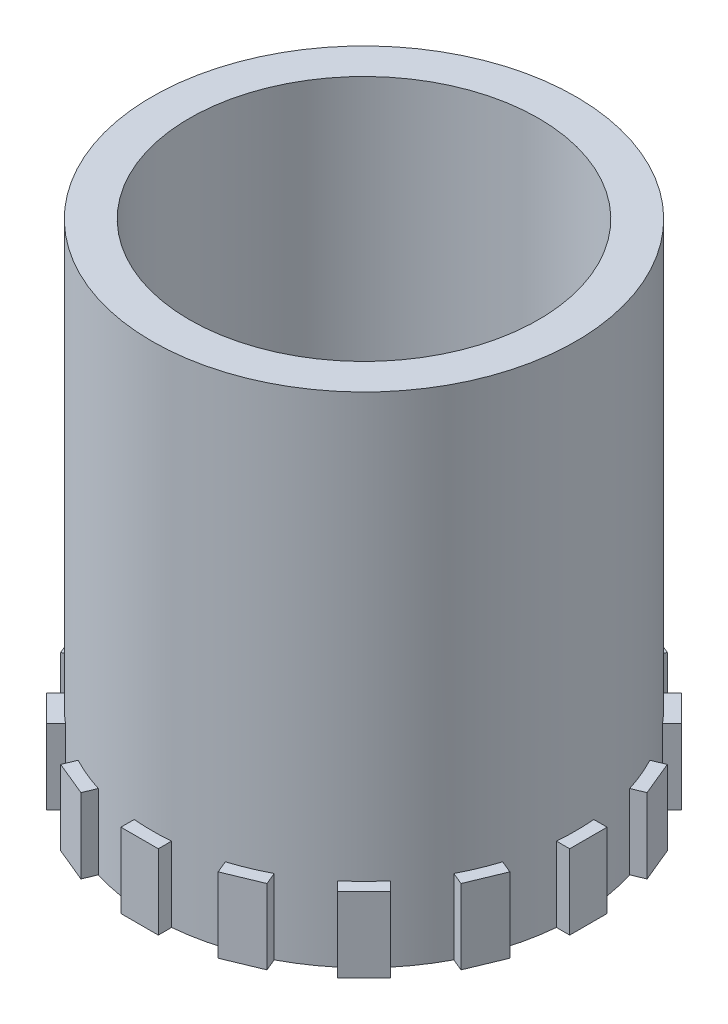
SolidWorks part; units mm, degrees
material "ABS"
ref_plane "前视基准面" through (0, 0, 0) normal (0, 0, 1) x (1, 0, 0)
ref_plane "上视基准面" through (0, 0, 0) normal (0, 1, 0) x (1, 0, 0)
ref_plane "右视基准面" through (0, 0, 0) normal (1, 0, 0) x (0, 0, -1)
sketch "草图1" plane through (0, 0, 0) normal (0, 1, 0) x (1, 0, 0)
  circle A0 centre (0, 0) radius 17
  circle A1 centre (0, 0) radius 14
  dimension "D1" = 34
  dimension "D2" = 28
extrude "凸台-拉伸1" add sketch "草图1" along normal blind 40
sketch "草图2" plane through (0, 0, 0) normal (0, -1, 0) x (-1, 0, 0)
  line L1 (-1.5, 16) -> (1.5, 16)
  line L2 (-1.5, 16) -> (-1.5, 18)
  line L3 (-1.5, 18) -> (1.5, 18)
  line L4 (1.5, 16) -> (1.5, 18)
  line L5 (-1.5, 16) -> (1.5, 18) construction
  line L6 (-1.5, 18) -> (1.5, 16) construction
  circle A0 centre (0, 0) radius 17 construction
  point P0 (0, 17)
  dimension "D1" = 3
  dimension "D2" = 2
extrude "凸台-拉伸2" add sketch "草图2" against normal blind 6
pattern_circular "阵列(圆周)1" count 16 over 360 about axis through (0, 0, 0) along (0, 1, 0) of "凸台-拉伸2"
